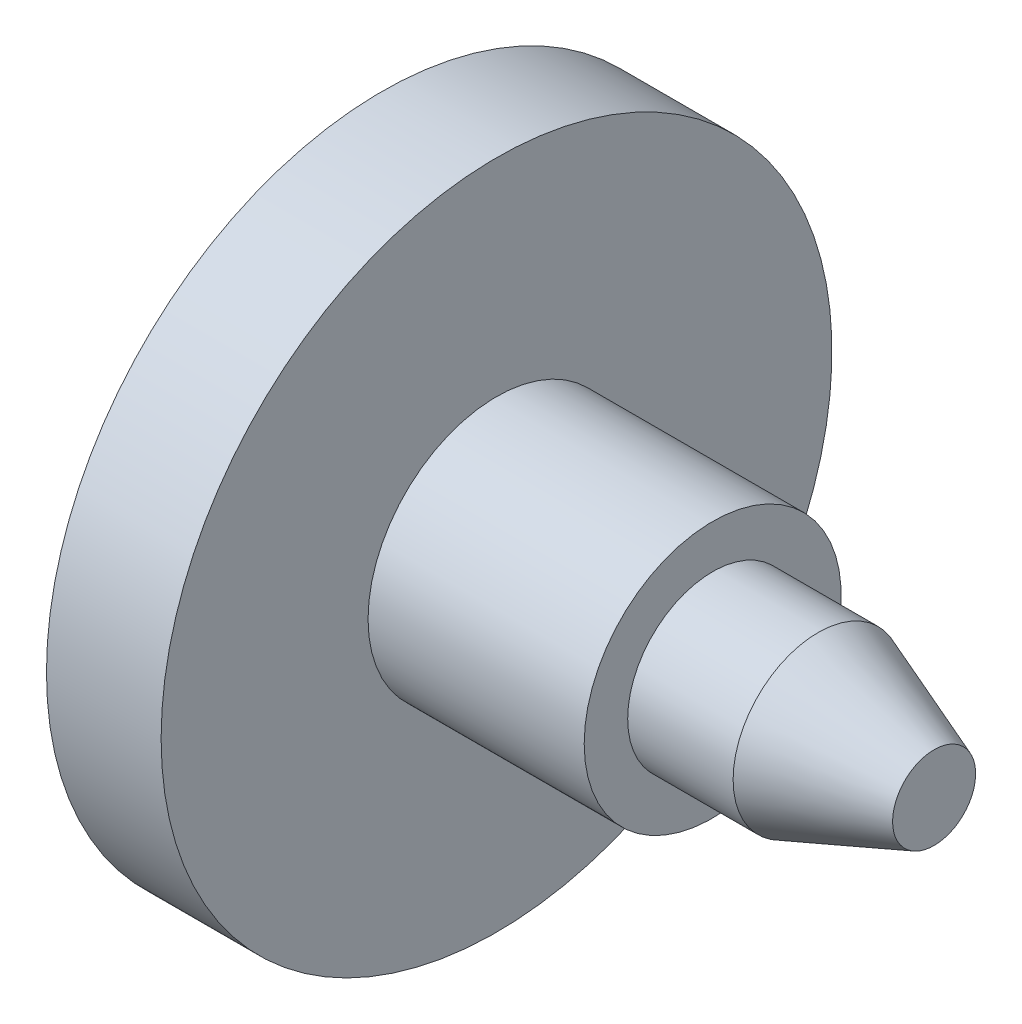
SolidWorks part; units mm, degrees
ref_plane "Front Plane" through (0, 0, 0) normal (0, 0, 1) x (1, 0, 0)
ref_plane "Top Plane" through (0, 0, 0) normal (0, 1, 0) x (1, 0, 0)
ref_plane "Right Plane" through (0, 0, 0) normal (1, 0, 0) x (0, 0, -1)
sketch "CL" plane through (0, 0, 0) normal (0, 0, 1) x (1, 0, 0)
  line L0 (-97.1656, 0) -> (122.2208, 0) construction
sketch "Sketch2" plane through (0, 0, 0) normal (0, 0, 1) x (1, 0, 0)
  line L0 (-23.1908, 67.8444) -> (-23.1908, 35.5883)
  line L1 (-23.1908, 35.5883) -> (-45.8516, 35.5883)
  line L2 (-45.8516, 35.5883) -> (-45.8516, 25.9915)
  line L3 (-45.8516, 25.9915) -> (-29.8584, 25.9915)
  line L4 (-29.8584, 25.9915) -> (-29.8584, 11.3296)
  line L5 (-29.8584, 11.3296) -> (60.3904, 11.3296)
  line L6 (60.3904, 11.3296) -> (78.6408, 5.4649)
  line L7 (78.6408, 5.4649) -> (78.6408, 0)
  line L8 (-97.1656, 0) -> (122.2208, 0) construction
  line L9 (78.6408, 0) -> (88.5043, 0)
  line L10 (88.5043, 0) -> (88.5043, 8.3972)
  line L11 (88.5043, 8.3972) -> (65.0453, 17.1944)
  line L14 (0, 67.8444) -> (-23.1908, 67.8444)
  line L15 (0, 67.8444) -> (0, 25.9915)
  line L16 (0, 25.9915) -> (43.719, 25.9915)
  line L17 (43.719, 25.9915) -> (43.719, 17.1944)
  line L18 (65.0453, 17.1944) -> (43.719, 17.1944)
revolve "Revolve1" add sketch "Sketch2" angle 360 about L0
